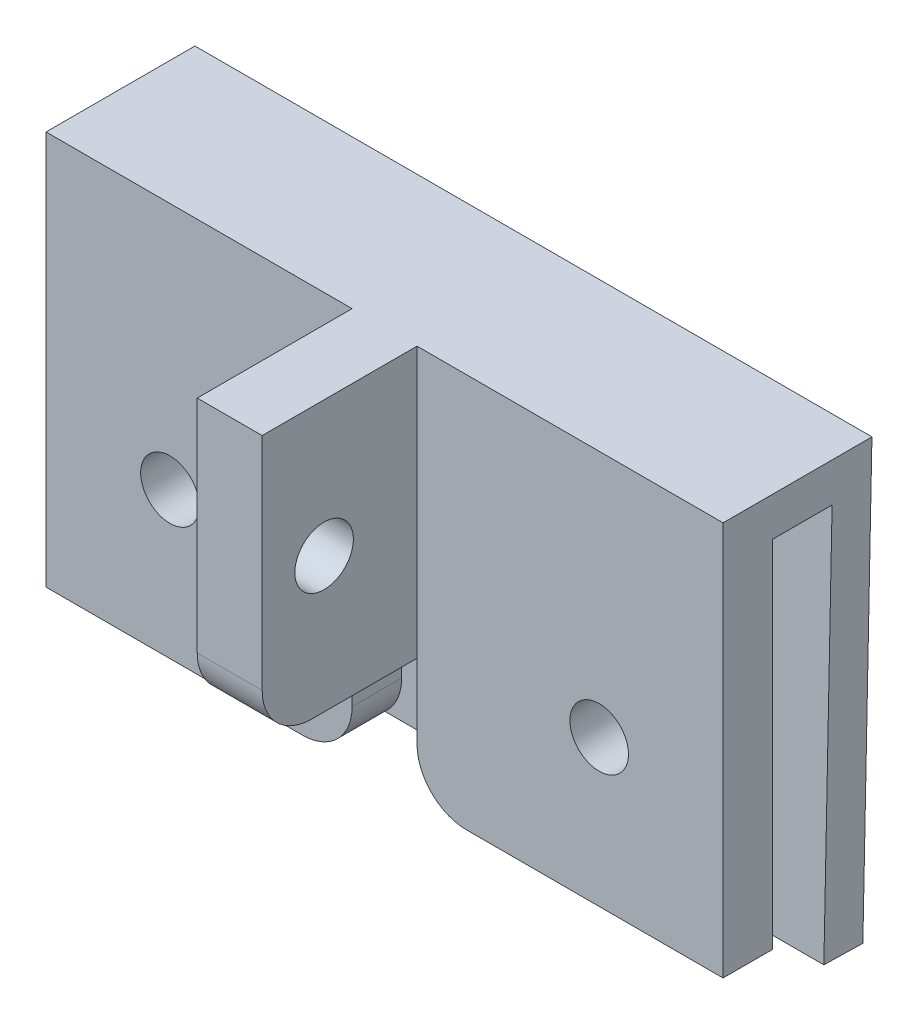
SolidWorks part; units mm, degrees
ref_plane "Front Plane" through (0, 0, 0) normal (0, 0, 1) x (1, 0, 0)
ref_plane "Top Plane" through (0, 0, 0) normal (0, 1, 0) x (1, 0, 0)
ref_plane "Right Plane" through (0, 0, 0) normal (1, 0, 0) x (0, 0, -1)
sketch "Sketch1" plane through (0, 0, 0) normal (0, 0, 1) x (1, 0, 0)
  line L0 (0, 10.102) -> (0, -10.102) construction
  line L1 (-17.35, 10.102) -> (17.35, 10.102)
  line L2 (-17.35, 10.102) -> (-17.35, -10.102)
  line L3 (-17.35, -10.102) -> (17.35, -10.102)
  line L4 (17.35, 10.102) -> (17.35, -10.102)
  line L5 (-17.35, -3.752) -> (17.35, -3.752) construction
  line L6 (-1.6637, -10.102) -> (-1.6637, -3.752)
  line L7 (-1.6637, -3.752) -> (1.6637, -3.752)
  line L8 (1.6637, -3.752) -> (1.6637, -10.102)
  line L9 (-11, -2.598) -> (11, -2.598) construction
  circle A0 centre (-11, -2.598) radius 1.5
  circle A1 centre (11, -2.598) radius 1.5
  point P14 (0, -3.752)
  point P19 (0, -2.598)
  point P23 (0, 0)
  dimension "D3" = 3
  dimension "D1" = 22
  dimension "D2" = 1.154
  dimension "D4" = 12.7
  dimension "D5" = 6.35
  dimension "D6" = 3.3274
  dimension "D7" = 6.35
extrude "Boss-Extrude1" add sketch "Sketch1" along normal blind 2.54 contours L7 L8 L3 L4 L1 L2 L6 A1 A0
sketch "Sketch2" plane through (0, 0, 2.54) normal (0, 0, 1) x (1, 0, 0)
  line L0 (-17.35, 10.102) -> (17.35, 10.102) construction
  line L1 (-1.6637, -3.752) -> (1.6637, -3.752)
  line L2 (-1.6637, -3.752) -> (-1.6637, 10.102)
  line L3 (-1.6637, 10.102) -> (1.6637, 10.102)
  line L4 (1.6637, -3.752) -> (1.6637, 10.102)
extrude "Boss-Extrude2" add sketch "Sketch2" along normal blind 7.9375
sketch "Sketch3" plane through (-1.6637, 0, 0) normal (-1, 0, 0) x (0, 0, 1)
  line L0 (10.4775, 10.102) -> (10.4775, -3.752) construction
  line L2 (2.54, 10.102) -> (2.54, -10.102) construction
  circle A1 centre (7.3025, 3.175) radius 1.5
  point P5 (10.4775, 3.175)
  dimension "D1" = 3
  dimension "D2" = 4.7625
extrude "Cut-Extrude1" cut sketch "Sketch3" against normal through all
fillet "Fillet1" radius 2.54 1 edges at (0, -3.752, 10.4775)
fillet "Fillet3" radius 2.54 2 edges at (1.6637, -10.102, 1.27) (-1.6637, -10.102, 1.27)
sketch "Sketch4" plane through (17.35, 0, 0) normal (1, 0, 0) x (0, 0, -1)
  line L0 (0, 10.102) -> (5.0903, 10.102)
  line L1 (5.0903, 10.102) -> (4.6666, -10.1438)
  line L2 (4.6666, -10.1438) -> (2.667, -10.102)
  line L3 (2.667, -10.102) -> (3.048, 8.102)
  line L4 (3.048, 8.102) -> (0, 8.102)
  line L5 (0, 10.102) -> (0, -10.102) construction
  line L6 (4.6666, -10.1438) -> (4.6247, -12.1434)
  line L7 (4.6247, -12.1434) -> (2.6252, -12.1016)
  line L8 (2.6252, -12.1016) -> (2.667, -10.102)
  line M9 (0, -10.102) -> (0, 10.102)
  dimension "D1" = 2
  dimension "D2" = 2
  dimension "D3" = 3.048
  dimension "D4" = 2.667
  dimension "D5" = 2
extrude "Boss-Extrude3" add sketch "Sketch4" against normal up to surface (34.7 mm away) contours L8 L7 L6 L2 | L4 L3 L2 L1 L0 M9 up to face at (-17.35, 0, 1.27)
equation "\"bottomThickness\"= .220in"
equation "\"wallThickness\"= .125in"
equation "\"D6@Sketch1\"=\"wallThickness\"+.006in"
equation "\"D3@Sketch4\"=\"wallThickness\"-.005in"
equation "\"D4@Sketch4\"=\"wallThickness\"-.02in"
